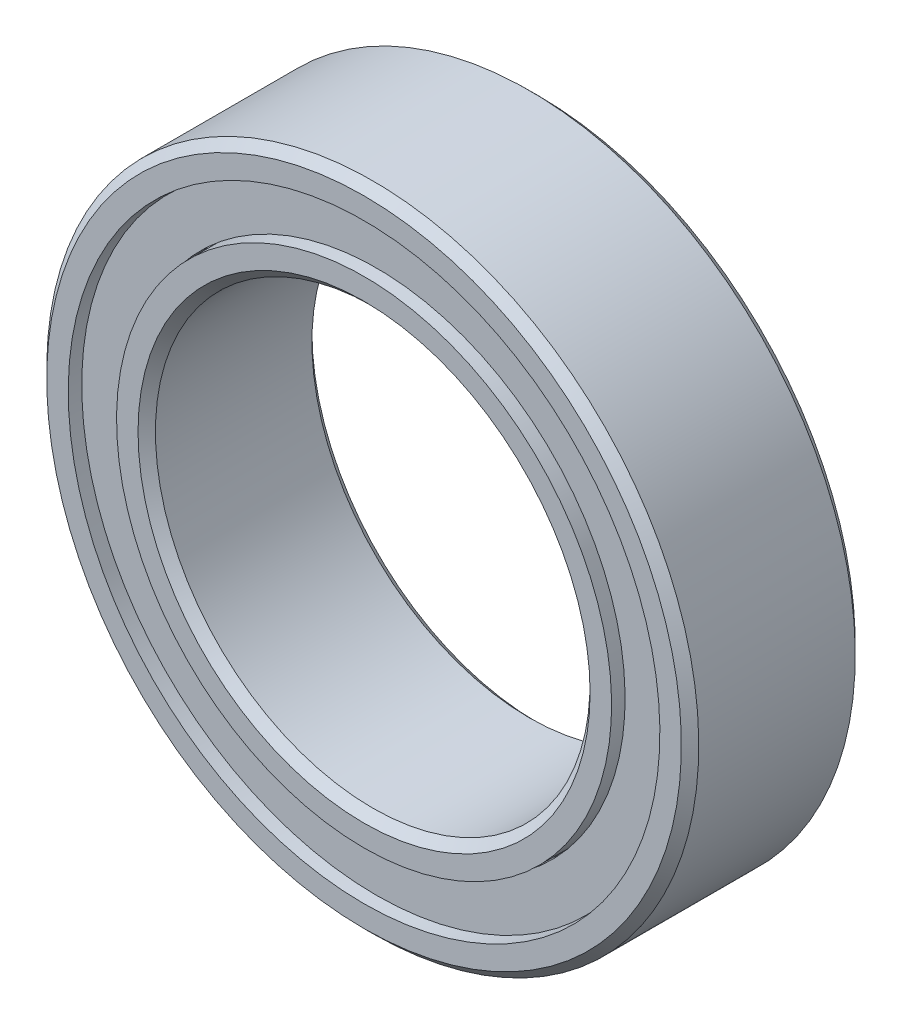
SolidWorks part; units mm, degrees
ref_plane "Front Plane" through (0, 0, 0) normal (0, 0, 1) x (1, 0, 0)
ref_plane "Top Plane" through (0, 0, 0) normal (0, 1, 0) x (1, 0, 0)
ref_plane "Right Plane" through (0, 0, 0) normal (1, 0, 0) x (0, 0, -1)
sketch "Sketch1" plane through (0, 0, 0) normal (0, 0, 1) x (1, 0, 0)
  circle A0 centre (0, 0) radius 7.5
  circle A1 centre (0, 0) radius 5
  dimension "OD" = 15
  dimension "ID" = 10
  dimension "For Shaft Diameter" = 10
  dimension "For Housing ID" = 15
sketch "Sketch8" plane through (0, 0, 0) normal (1, 0, 0) x (0, 0, -1)
  line L1 (-2, 7.5) -> (2, 7.5)
  line L2 (-2, 7.5) -> (-2, -7.5)
  line L3 (-2, -7.5) -> (2, -7.5)
  line L4 (2, 7.5) -> (2, -7.5)
  line L5 (-2, 7.5) -> (2, -7.5) construction
  line L6 (-2, -7.5) -> (2, 7.5) construction
  point P0 (0, 0)
  point P6 (0, -7.5)
  dimension "Width" = 4
sketch "Sketch5" plane through (0, 0, 0) normal (1, 0, 0) x (0, 0, -1)
  line L0 (-2, 0) -> (2, 0) construction
  line L1 (0, 7.5) -> (0, -7.5) construction
  line L2 (1.8, 7.5) -> (-1.8, 7.5)
  line L3 (-1.8, 7.5) -> (-2, 7.3)
  line L4 (-2, 7.3) -> (-2, 6.8056)
  line L5 (-2, 6.8056) -> (-0.8889, 6.8056)
  line L6 (2, 6.8056) -> (0.8889, 6.8056)
  line L7 (2, 7.3) -> (2, 6.8056)
  line L8 (1.8, 7.5) -> (2, 7.3)
  line L9 (0, 7.5) -> (0, 6.25) construction
  line L10 (0, 6.25) -> (0, 5) construction
  line L11 (-1.0482, 6.25) -> (-2, 6.25) construction
  line L12 (1.3336, 5.7198) -> (1.7146, 5.7198)
  line L13 (-1.3336, 5.7198) -> (-1.7146, 5.7198)
  line L14 (-1.3336, 5.7198) -> (-1.3336, 6.7802)
  line L15 (-1.3336, 6.7802) -> (-1.7146, 6.7802)
  line L16 (-1.7146, 5.7198) -> (-1.7146, 6.7802)
  line L17 (-1.3336, 5.7198) -> (-1.7146, 6.7802) construction
  line L18 (-1.3336, 6.7802) -> (-1.7146, 5.7198) construction
  line L19 (1.7146, 5.7198) -> (1.7146, 6.7802)
  line L20 (1.3336, 6.7802) -> (1.7146, 6.7802)
  line L21 (1.3336, 5.7198) -> (1.3336, 6.7802)
  line L22 (0, 7.5) -> (0, -7.5) construction
  line L23 (2, 0) -> (2, 7.5) construction
  line L24 (2, 7.5) -> (1.8, 7.5) construction
  line L25 (-2, 0) -> (-2, 7.5) construction
  line L26 (-2, 7.5) -> (-1.8, 7.5) construction
  line L27 (2, 0) -> (2, -7.5) construction
  line L28 (-2, 0) -> (-2, -7.5) construction
  line L29 (-2, -7.5) -> (2, -7.5) construction
  arc A0 (-0.8889, 6.8056) -> (0.8889, 6.8056) centre (0, 6.25) cw
  circle A1 centre (0, 6.25) radius 1.0482 construction
  point P14 (0, 5)
  point P15 (-1.5241, 6.25)
  dimension "D1" = 45
  dimension "D2" = 0.2
  dimension "D3" = 1.7778
  dimension "D4" = 0.5556
  dimension "D5" = 0.381
  dimension "D6" = 0.0254
revolve "Revolve1" add sketch "Sketch5" angle 360 about L0
sketch "Sketch3" plane through (0, 0, 0) normal (1, 0, 0) x (0, 0, -1)
  line L0 (-2, 5.6944) -> (-0.8889, 5.6944)
  line L1 (0, 7.5) -> (0, -7.5) construction
  line L2 (-2, 7.3) -> (-2, 6.8056) construction
  line L3 (-2, 5.6944) -> (-2, 5.2)
  line L4 (-1.8, 7.5) -> (-2, 7.3) construction
  line L5 (-2, 5.2) -> (-1.8, 5)
  line L6 (-1.8, 5) -> (1.8, 5)
  line L7 (1.8, 7.5) -> (1.8, -7.5) construction
  line L8 (1.8, 5) -> (2, 5.2)
  line L9 (2, -7.3) -> (2, 7.3) construction
  line L10 (2, 5.2) -> (2, 5.6944)
  line L11 (2, 5.6944) -> (0.8889, 5.6944)
  line L13 (1.8, 7.5) -> (2, 7.3) construction
  arc A0 (0.8889, 6.8056) -> (-0.8889, 6.8056) centre (0, 6.25) ccw construction
  arc A1 (0.8889, 5.6944) -> (-0.8889, 5.6944) centre (0, 6.25) cw
revolve "Revolve3" add sketch "Sketch3" angle 360 about L0
sketch "Sketch4" plane through (0, 0, 0) normal (1, 0, 0) x (0, 0, -1)
  line L0 (-1.0482, 6.25) -> (1.0482, 6.25)
  arc A2 (-1.0482, 6.25) -> (1.0482, 6.25) centre (0, 6.25) cw
  arc A3 (0.8889, 6.8056) -> (-0.8889, 6.8056) centre (0, 6.25) ccw construction
revolve "Revolve4" add sketch "Sketch4" angle 360 about L0
pattern_circular "CirPattern1" count 11 every 32.727 about axis through (0, 0, 0) along (0, 0, 1) of bodies 104
equation "\"D2@Sketch5\" = \"Width@Sketch8\" * .05"
equation "\"D3@Sketch5\" = \"Width@Sketch8\" / 2.25"
equation "\"D4@Sketch5\"=((\"OD@Sketch1\"-\"ID@Sketch1\")/2)/4.5"
equation "\"D2@CirPattern1\" = 360/\"Balls@CirPattern1\""
